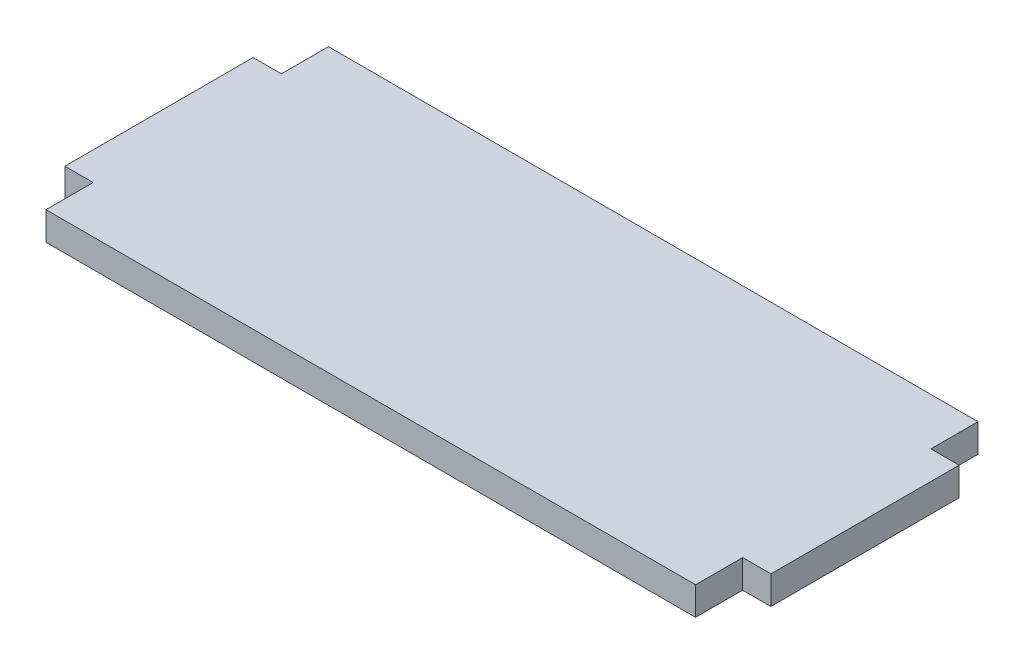
SolidWorks part; units mm, degrees
ref_plane "Front Plane" through (0, 0, 0) normal (0, 0, 1) x (1, 0, 0)
ref_plane "Top Plane" through (0, 0, 0) normal (0, 1, 0) x (1, 0, 0)
ref_plane "Right Plane" through (0, 0, 0) normal (1, 0, 0) x (0, 0, -1)
sketch "Sketch1" plane through (0, 0, 0) normal (0, 1, 0) x (1, 0, 0)
  line L0 (0, 25) -> (0, 30)
  line L1 (0, 0) -> (69, 0)
  line L3 (0, 30) -> (69, 30)
  line L5 (0, 25) -> (-3, 25)
  line L7 (0, 5) -> (-3, 5)
  line L8 (-3, 25) -> (-3, 5)
  line L9 (69, 25) -> (72, 25)
  line L11 (69, 5) -> (72, 5)
  line L12 (72, 25) -> (72, 5)
  line L13 (0, 5) -> (0, 0)
  line L16 (69, 25) -> (69, 30)
  line L17 (69, 5) -> (69, 0)
  point P13 (0, 0)
extrude "Boss-Extrude1" add sketch "Sketch1" along normal blind 3 contours L17 L1 L13 L7 L8 L5 L0 L3 L16 L9 L12 L11
